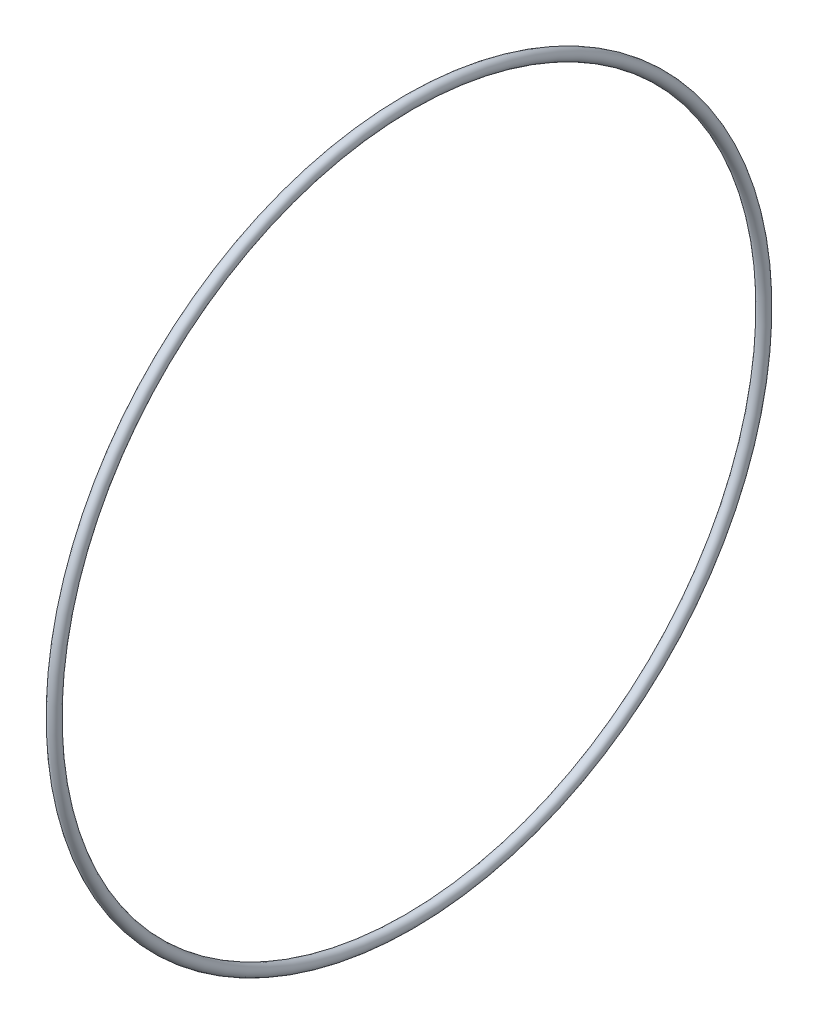
SolidWorks part; units mm, degrees
material "6061-T6 (SS)"
ref_plane "Front Plane" through (0, 0, 0) normal (0, 0, 1) x (1, 0, 0)
ref_plane "Top Plane" through (0, 0, 0) normal (0, 1, 0) x (1, 0, 0)
ref_plane "Right Plane" through (0, 0, 0) normal (1, 0, 0) x (0, 0, -1)
sketch "Sketch1" plane through (0, 0, 0) normal (0, 0, 1) x (1, 0, 0)
  line L0 (0, 0) -> (0, 796.0995) construction
  line L2 (0, 0) -> (241.303, 0) construction
  circle A0 centre (0, 796.0995) radius 12.7
  circle A1 centre (0, 796.0995) radius 10.3187
  point P6 (0, 783.3995)
  dimension "D1" = 25.4
  dimension "D3" = 796.0995
  dimension "D4" = 783.3995
  dimension "D2" = 2.3813
revolve "Revolve1" add sketch "Sketch1" angle 360 about L2
